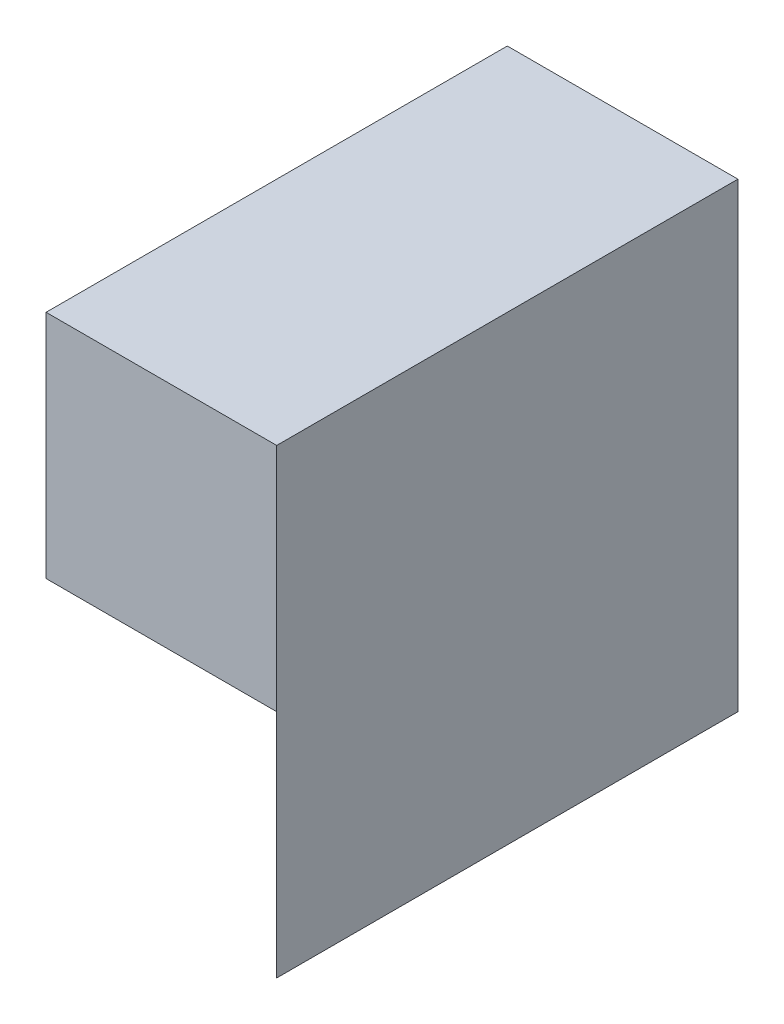
SolidWorks part; units mm, degrees
ref_plane "Front Plane" through (0, 0, 0) normal (0, 0, 1) x (1, 0, 0)
ref_plane "Top Plane" through (0, 0, 0) normal (0, 1, 0) x (1, 0, 0)
ref_plane "Right Plane" through (0, 0, 0) normal (1, 0, 0) x (0, 0, -1)
sketch "Sketch1" plane through (0, 0, 0) normal (0, 0, 1) x (1, 0, 0)
  line L1 (0, 0) -> (40, 0)
  line L2 (0, 0) -> (0, 20)
  line L3 (0, 20) -> (40, 20)
  line L4 (40, 0) -> (40, 20)
  dimension "D1" = 40
  dimension "D2" = 20
extrude "Boss-Extrude1" add sketch "Sketch1" along normal blind 40
sketch "Sketch2" plane through (0, 0, 40) normal (0, 0, 1) x (1, 0, 0)
  line L1 (40, 20) -> (20, 20)
  line L2 (40, 20) -> (40, 40)
  line L3 (40, 40) -> (20, 40)
  line L4 (20, 20) -> (20, 40)
  dimension "D1" = 20
  dimension "D2" = 20
extrude "Boss-Extrude2" add sketch "Sketch2" against normal blind 40
sketch "Sketch3" plane through (0, 40, 0) normal (0, 1, 0) x (1, 0, 0)
  line L0 (20, -40) -> (40, -20)
  line L1 (40, 0) -> (40, -40) construction
  line L2 (40, -20) -> (40, -40)
  line L3 (40, -40) -> (20, -40)
extrude "Cut-Extrude1" cut sketch "Sketch3" against normal blind 20
sketch "Sketch4" plane through (20, 0, 0) normal (-1, 0, 0) x (0, 0, 1)
  line L1 (0, 20) -> (40, 20)
  line L2 (0, 20) -> (0, 40)
  line L3 (0, 40) -> (40, 40)
  line L4 (40, 20) -> (40, 40)
extrude "Cut-Extrude2" cut sketch "Sketch4" against normal blind 35
sketch "Sketch5" plane through (0, 20, 0) normal (0, 1, 0) x (1, 0, 0)
  line L0 (0, 0) -> (40, -40)
  line L1 (40, -40) -> (0, -40)
  line L2 (0, -40) -> (0, 0)
extrude "Cut-Extrude3" cut sketch "Sketch5" against normal blind 35
sketch "Sketch6" plane through (0, 20, 0) normal (0, 1, 0) x (1, 0, 0)
  line L1 (40, 0) -> (20, 0)
  line L2 (40, 0) -> (40, -40)
  line L3 (40, -40) -> (20, -40)
  line L4 (20, 0) -> (20, -40)
  dimension "D1" = 40
  dimension "D2" = 20
extrude "Boss-Extrude3" add sketch "Sketch6" along normal blind 20
